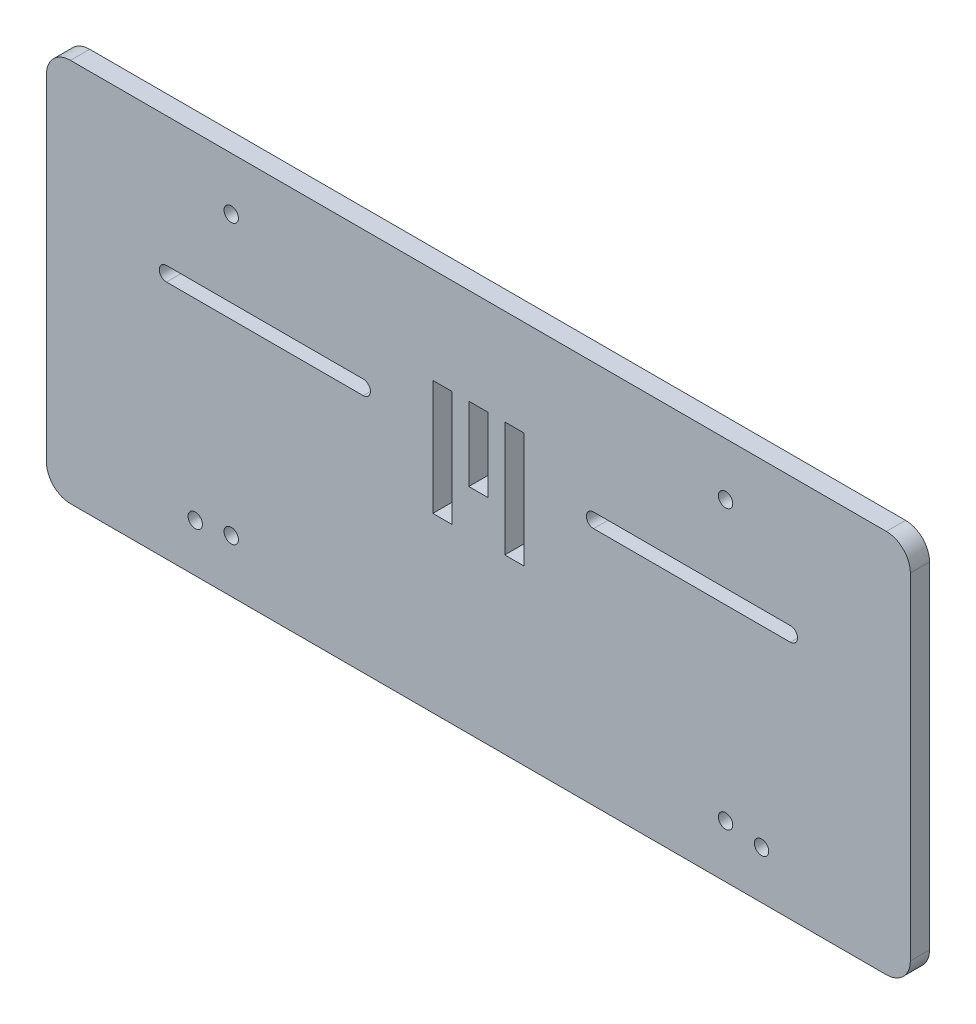
SolidWorks part; units mm, degrees
material "Acrylic (Medium-high impact)"
ref_plane "Front Plane" through (0, 0, 0) normal (0, 0, 1) x (1, 0, 0)
ref_plane "Top Plane" through (0, 0, 0) normal (0, 1, 0) x (1, 0, 0)
ref_plane "Right Plane" through (0, 0, 0) normal (1, 0, 0) x (0, 0, -1)
sketch "Sketch1" plane through (0, 0, 0) normal (0, 0, 1) x (1, 0, 0)
  line L0 (-62.2994, -8.1171) -> (-21.2994, -8.1171)
  line L1 (-21.2994, -11.1171) -> (-62.2994, -11.1171)
  line L2 (-87.2994, 18.8829) -> (92.7006, 18.8829)
  line L3 (-87.2994, 18.8829) -> (-87.2994, -61.1171)
  line L4 (-87.2994, -61.1171) -> (92.7006, -61.1171)
  line L5 (92.7006, 18.8829) -> (92.7006, -61.1171)
  line L6 (26.7006, -8.1171) -> (67.7006, -8.1171)
  line L7 (67.7006, -11.1171) -> (26.7006, -11.1171)
  arc A0 (-62.2994, -8.1171) -> (-62.2994, -11.1171) centre (-62.2994, -9.6171) ccw
  arc A1 (26.7006, -8.1171) -> (26.7006, -11.1171) centre (26.7006, -9.6171) ccw
  circle A2 centre (61.7006, -51.1171) radius 1.5
  circle A3 centre (-56.2994, -51.1171) radius 1.5
  arc A4 (-21.2994, -11.1171) -> (-21.2994, -8.1171) centre (-21.2994, -9.6171) ccw
  arc A5 (67.7006, -11.1171) -> (67.7006, -8.1171) centre (67.7006, -9.6171) ccw
  circle A10 centre (-48.7994, 7.8829) radius 1.5
  circle A11 centre (54.2006, 7.8829) radius 1.5
  circle A12 centre (54.2006, -50.1171) radius 1.5
  circle A13 centre (-48.7994, -50.1171) radius 1.5
  dimension "D10" = 180
  dimension "D16" = 2
  dimension "D20" = 11
  dimension "D2" = 31
  dimension "D3" = 31
  dimension "D7" = 80
  dimension "D8" = 10
  dimension "D9" = 10
  dimension "D19" = 38.5
  dimension "D18" = 2
extrude "Boss-Extrude1" add sketch "Sketch1" along normal blind 4
sketch "Sketch2" plane through (0, 0, 4) normal (0, 0, 1) x (1, 0, 0)
  line L1 (-6.7994, -1.1171) -> (-2.7994, -1.1171)
  line L2 (-6.7994, -1.1171) -> (-6.7994, -25.1171)
  line L3 (-6.7994, -25.1171) -> (-2.7994, -25.1171)
  line L4 (-2.7994, -1.1171) -> (-2.7994, -25.1171)
  line L5 (0.7006, -1.1171) -> (4.7006, -1.1171)
  line L6 (0.7006, -1.1171) -> (0.7006, -16.5171)
  line L7 (0.7006, -16.5171) -> (4.7006, -16.5171)
  line L8 (4.7006, -1.1171) -> (4.7006, -16.5171)
  line L12 (12.2006, -1.1171) -> (12.2006, -25.1171)
  line L13 (8.2006, -1.1171) -> (12.2006, -1.1171)
  line L14 (8.2006, -1.1171) -> (8.2006, -25.1171)
  line L15 (8.2006, -25.1171) -> (12.2006, -25.1171)
  line L16 (92.7006, 18.8829) -> (-87.2994, 18.8829) construction
  dimension "D1" = 20
  dimension "D2" = 2
  dimension "D4" = 20
extrude "Cut-Extrude1" cut sketch "Sketch2" against normal blind 4
fillet "Fillet1" radius 5 4 edges at (-87.2994, 18.8829, 2) (-87.2994, -61.1171, 2) (92.7006, -61.1171, 2) (92.7006, 18.8829, 2)
